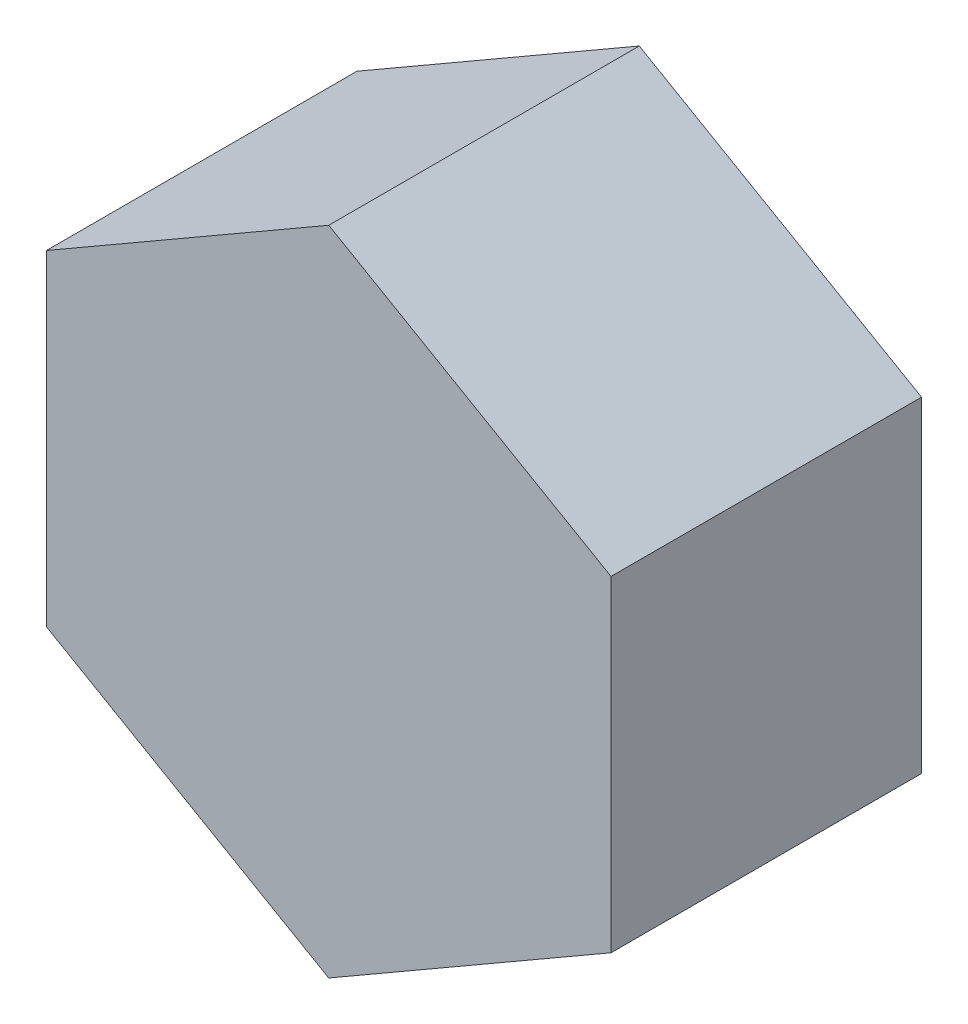
SolidWorks part; units mm, degrees
material "ASTM A36 Steel"
ref_plane "Front Plane" through (0, 0, 0) normal (0, 0, 1) x (1, 0, 0)
ref_plane "Top Plane" through (0, 0, 0) normal (0, 1, 0) x (1, 0, 0)
ref_plane "Right Plane" through (0, 0, 0) normal (1, 0, 0) x (0, 0, -1)
sketch "Sketch1" plane through (0, 0, 0) normal (0, 0, 1) x (1, 0, 0)
  line L1 (0, 14.6647) -> (-12.7, 7.3323)
  line L2 (-12.7, 7.3323) -> (-12.7, -7.3323)
  line L3 (-12.7, -7.3323) -> (0, -14.6647)
  line L4 (0, -14.6647) -> (12.7, -7.3323)
  line L5 (12.7, -7.3323) -> (12.7, 7.3323)
  line L6 (12.7, 7.3323) -> (0, 14.6647)
  circle A0 centre (0, 0) radius 12.7 construction
  dimension "D1" = 25.4
extrude "Boss-Extrude1" add sketch "Sketch1" along normal blind 13.97
sketch "Sketch4" plane through (0, 0, 0) normal (1, 0, 0) x (0, 0, -1)
  line L2 (0, 5.4799) -> (0, 10.0673)
  line L3 (0, 7.3323) -> (0, 14.6647) construction
  line L4 (0, 10.0673) -> (2.7701, 10.0673)
  line L5 (2.7701, 10.0673) -> (2.7701, 0)
  line L6 (-9.9299, 0) -> (2.7701, 0)
  arc A0 (-0.1947, 5.3724) -> (-9.9299, 0) centre (-3.5799, 0) ccw
  arc A1 (0, 5.4799) -> (-0.1947, 5.3724) centre (-0.127, 5.4799) cw
  dimension "D1" = 12.7
  dimension "D2" = 0.127
revolve "Cut-Revolve1" cut sketch "Sketch4" angle 360 about L6
